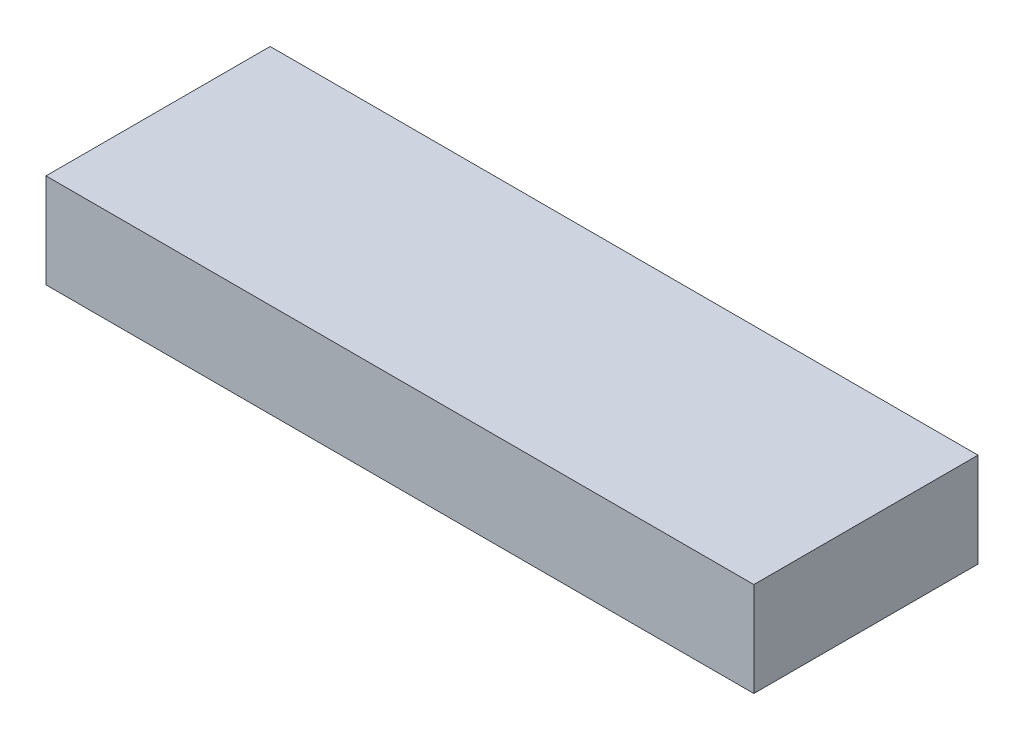
SolidWorks part; units mm, degrees
ref_plane "Front Plane" through (0, 0, 0) normal (0, 0, 1) x (1, 0, 0)
ref_plane "Top Plane" through (0, 0, 0) normal (0, 1, 0) x (1, 0, 0)
ref_plane "Right Plane" through (0, 0, 0) normal (1, 0, 0) x (0, 0, -1)
sketch "Sketch1" plane through (0, 0, 0) normal (0, 1, 0) x (1, 0, 0)
  line L1 (-30, 9.5) -> (30, 9.5)
  line L2 (-30, 9.5) -> (-30, -9.5)
  line L3 (-30, -9.5) -> (30, -9.5)
  line L4 (30, 9.5) -> (30, -9.5)
  line L5 (-30, 9.5) -> (30, -9.5) construction
  line L6 (-30, -9.5) -> (30, 9.5) construction
  point P0 (0, 0)
  dimension "D1" = 60
  dimension "D2" = 19
extrude "Boss-Extrude1" add sketch "Sketch1" along normal blind 8
